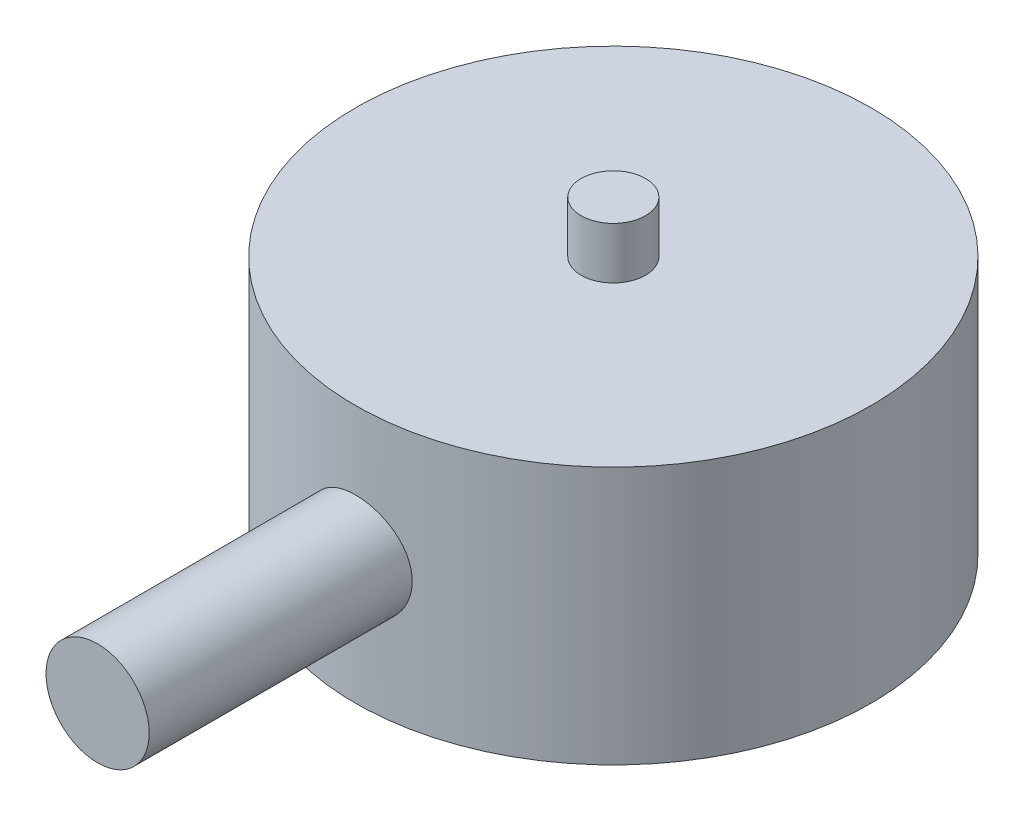
SolidWorks part; units mm, degrees
ref_plane "Front Plane" through (0, 0, 0) normal (0, 0, 1) x (1, 0, 0)
ref_plane "Top Plane" through (0, 0, 0) normal (0, 1, 0) x (1, 0, 0)
ref_plane "Right Plane" through (0, 0, 0) normal (1, 0, 0) x (0, 0, -1)
sketch "Sketch1" plane through (0, 0, 0) normal (0, 0, 1) x (1, 0, 0)
  line L0 (0, 0) -> (0, -12)
  line L1 (0, 0) -> (1.25, 0)
  line L2 (1.25, 0) -> (1.25, -2)
  line L3 (1.25, -2) -> (10, -2)
  line L4 (10, -2) -> (10, -12)
  line L5 (10, -12) -> (0, -12)
  line L6 (0, 0) -> (0, 6.4484) construction
  dimension "D1" = 20
  dimension "D2" = 2.5
  dimension "D3" = 12
  dimension "D4" = 10
revolve "Revolve1" add sketch "Sketch1" angle 360 about L6
sketch "Sketch2" plane through (0, 0, 0) normal (0, 0, 1) x (1, 0, 0)
  line L0 (0, -2) -> (0, -12) construction
  line L1 (10, -2) -> (-10, -2) construction
  line L2 (-10, -12) -> (10, -12) construction
  circle A0 centre (0, -7) radius 2
  point P8 (0, -7)
  dimension "D1" = 4
extrude "Boss-Extrude1" add sketch "Sketch2" along normal blind 20
